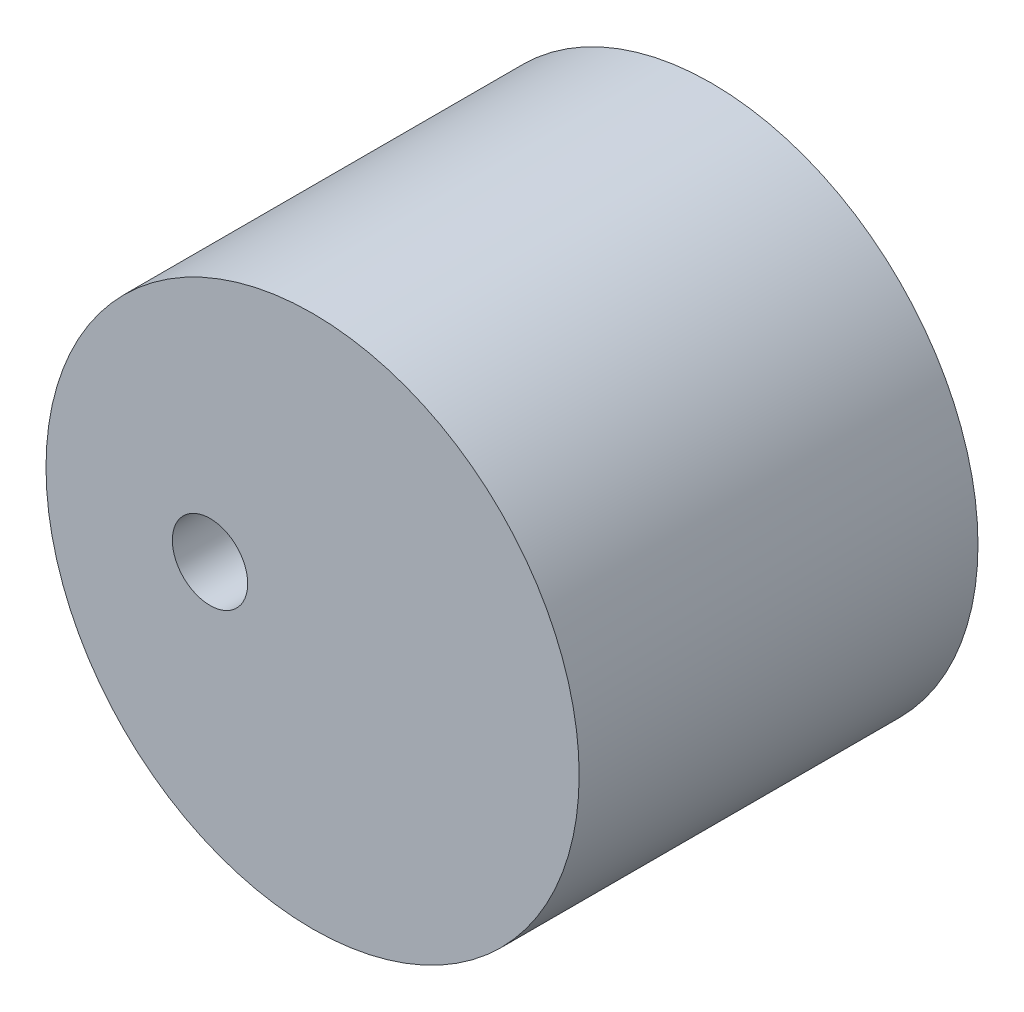
SolidWorks part; units mm, degrees
ref_plane "Front Plane" through (0, 0, 0) normal (0, 0, 1) x (1, 0, 0)
ref_plane "Top Plane" through (0, 0, 0) normal (0, 1, 0) x (1, 0, 0)
ref_plane "Right Plane" through (0, 0, 0) normal (1, 0, 0) x (0, 0, -1)
sketch "Sketch11" plane through (0, 0, 0) normal (0, 0, 1) x (1, 0, 0)
  circle A0 centre (0, 0) radius 23.3938
  circle A1 centre (-9, 0) radius 3.3085
  point P4 (0, 0)
  point P5 (0, 0)
extrude "Boss-Extrude13" add sketch "Sketch11" along normal blind 35
